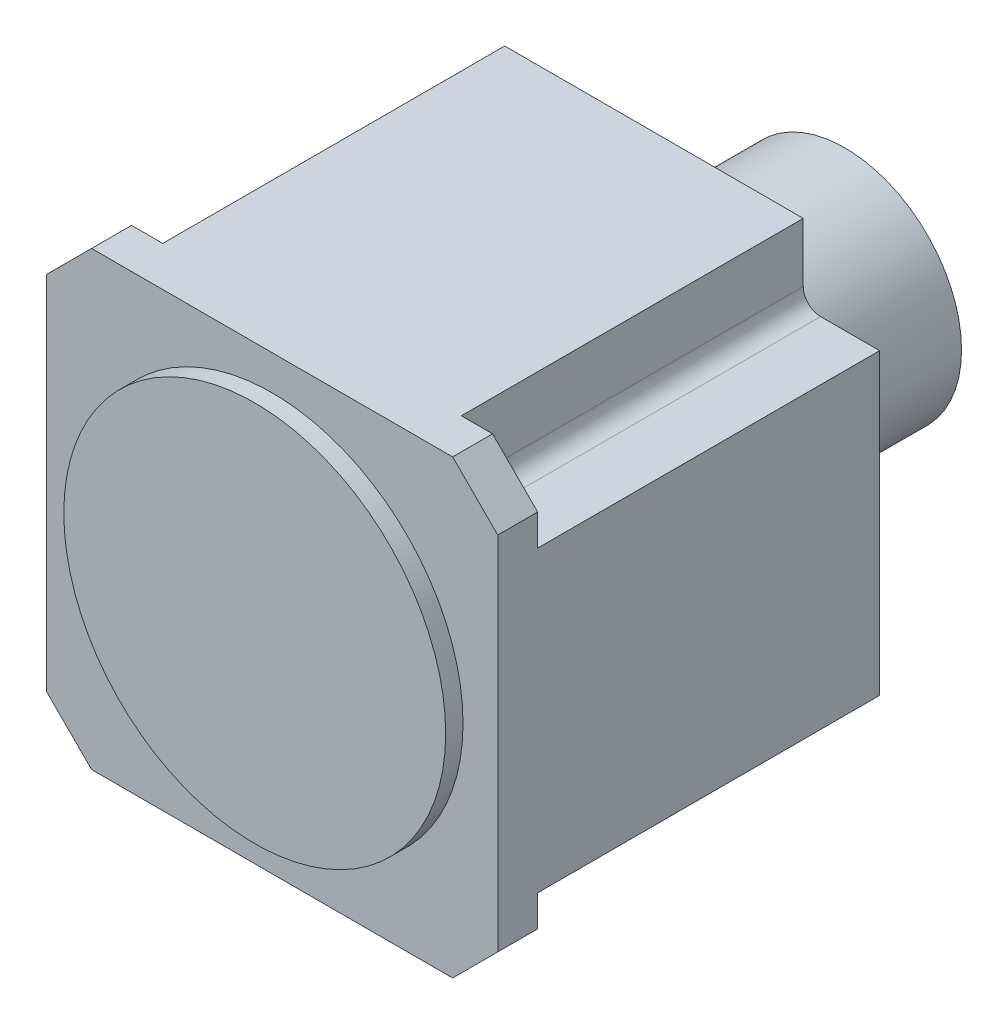
SolidWorks part; units mm, degrees
ref_plane "前视基准面" through (0, 0, 0) normal (0, 0, 1) x (1, 0, 0)
ref_plane "上视基准面" through (0, 0, 0) normal (0, 1, 0) x (1, 0, 0)
ref_plane "右视基准面" through (0, 0, 0) normal (1, 0, 0) x (0, 0, -1)
other "Configuration Table"
sketch "草图1" plane through (0, 0, 0) normal (0, 0, 1) x (1, 0, 0)
  line L0 (0, -117) -> (-117, 0)
  line L1 (65, 65) -> (-65, 65)
  line L2 (65, 65) -> (65, -65)
  line L3 (65, -65) -> (-65, -65)
  line L4 (-65, 65) -> (-65, -65)
  line L5 (65, 65) -> (-65, -65) construction
  line L6 (65, -65) -> (-65, 65) construction
  line L7 (0, -117) -> (117, 0)
  line L8 (-117, 0) -> (0, 117)
  line L9 (117, 0) -> (0, 117)
  line L10 (0, -117) -> (0, 117) construction
  line L11 (-117, 0) -> (117, 0) construction
  point P0 (0, 0)
  point P7 (0, 0)
  point P8 (-52, 65)
  dimension "D1" = 130
  dimension "D2" = 130
  dimension "D3" = 13
extrude "凸台-拉伸1" add sketch "草图1" along normal blind 11.5 contours L2 L9 L1 L8 L4 L0 L3 L7
sketch "草图2" plane through (0, 0, 11.5) normal (0, 0, 1) x (1, 0, 0)
  circle A0 centre (0, 0) radius 55
  dimension "D1" = 110
extrude "凸台-拉伸2" add sketch "草图2" along normal blind 5
sketch "草图5" plane through (0, 0, 0) normal (0, 0, -1) x (-1, 0, 0)
  line L0 (-65, 52) -> (-65, -52) construction
  line L1 (65, -43) -> (-65, -43)
  line L2 (65, -43) -> (65, 43)
  line L3 (65, 43) -> (-65, 43)
  line L4 (-65, -43) -> (-65, 43)
  line L5 (65, -43) -> (-65, 43) construction
  line L6 (65, 43) -> (-65, -43) construction
  line L7 (-52, 65) -> (52, 65) construction
  line L8 (43, -65) -> (-43, -65)
  line L9 (43, -65) -> (43, 65)
  line L10 (43, 65) -> (-43, 65)
  line L11 (-43, -65) -> (-43, 65)
  line L12 (43, -65) -> (-43, 65) construction
  line L13 (43, 65) -> (-43, -65) construction
  point P0 (0, 0)
  point P8 (0, 0)
  line M9 (-65, 52) -> (-65, -52)
  line M11 (-52, -65) -> (52, -65)
  line M13 (65, -52) -> (65, 52)
  line M15 (52, 65) -> (-52, 65)
  dimension "D1" = 22
extrude "凸台-拉伸4" add sketch "草图5" along normal blind 98.5 contours L11 L3 L9 M15 | L1 L11 L3 M9 | L11 L1 L9 L3 | L9 L1 L3 M13 | L11 L9 L1 M11
fillet "圆角1" radius 5 4 edges at (43, -43, -49.25) (-43, -43, -49.25) (-43, 43, -49.25) (43, 43, -49.25)
sketch "草图6" plane through (0, 0, -98.5) normal (0, 0, -1) x (-1, 0, 0)
  circle A0 centre (0, 0) radius 33.6
  dimension "D1" = 67.2
extrude "凸台-拉伸5" add sketch "草图6" along normal blind 55
